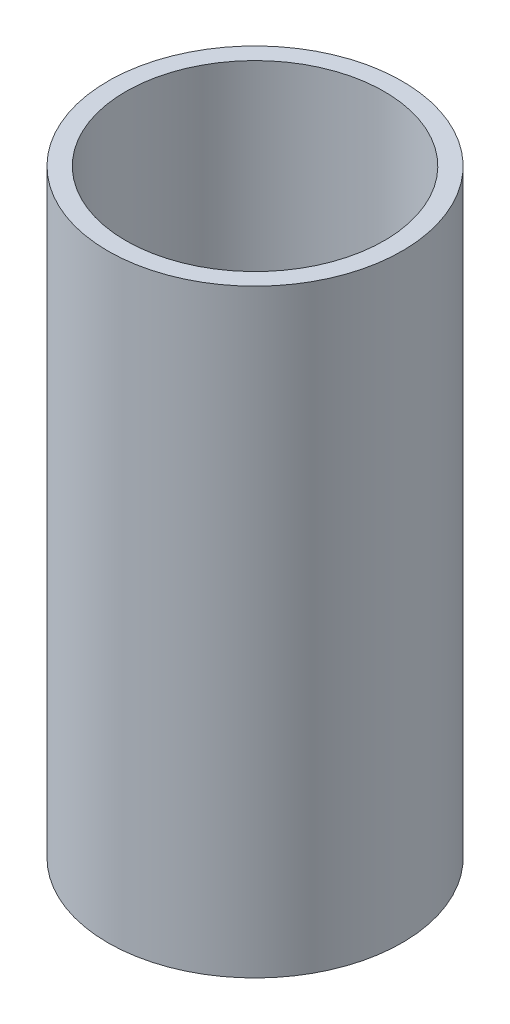
SolidWorks part; units mm, degrees
material "PVC Rigid"
ref_plane "Front Plane" through (0, 0, 0) normal (0, 0, 1) x (1, 0, 0)
ref_plane "Top Plane" through (0, 0, 0) normal (0, 1, 0) x (1, 0, 0)
ref_plane "Right Plane" through (0, 0, 0) normal (1, 0, 0) x (0, 0, -1)
sketch "Sketch1" plane through (0, 0, 0) normal (0, 1, 0) x (1, 0, 0)
  circle A0 centre (0, 0) radius 50.8
  circle A1 centre (0, 0) radius 57.837
  dimension "D1" = 101.6
extrude "Boss-Extrude1" add sketch "Sketch1" along normal blind 235.5
